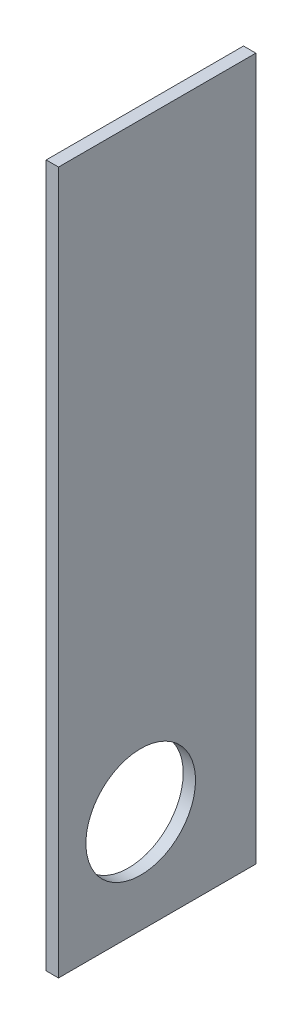
SolidWorks part; units mm, degrees
ref_plane "Front Plane" through (0, 0, 0) normal (0, 0, 1) x (1, 0, 0)
ref_plane "Top Plane" through (0, 0, 0) normal (0, 1, 0) x (1, 0, 0)
ref_plane "Right Plane" through (0, 0, 0) normal (1, 0, 0) x (0, 0, -1)
sketch "Sketch1" plane through (0, 0, 0) normal (1, 0, 0) x (0, 0, -1)
  line L1 (20.3921, -967.2196) -> (-267.6079, -967.2196)
  line L2 (20.3921, -967.2196) -> (20.3921, 57.7804)
  line L3 (20.3921, 57.7804) -> (-267.6079, 57.7804)
  line L4 (-267.6079, -967.2196) -> (-267.6079, -836.1219)
  line L5 (20.3921, -967.2196) -> (-267.6079, 57.7804) construction
  line L6 (20.3921, 57.7804) -> (-267.6079, -967.2196) construction
  line L7 (-267.6079, -676.1219) -> (-267.6079, 57.7804)
  line L10 (-267.6079, -676.1219) -> (-267.6079, -836.1219)
  circle A0 centre (-147.6079, -817.2196) radius 80
  point P0 (-123.6079, -454.7196)
  dimension "D3" = 160
  dimension "D4" = 120
  dimension "D1" = 288
  dimension "D2" = 1025
  dimension "D5" = 150
extrude "Boss-Extrude1" add sketch "Sketch1" along normal blind 18
equation "\"H_POLKI\"=1025"
equation "\"D2@Sketch1\"=\"H_POLKI\""
equation "\"DSP_WIDTH\"=18"
equation "\"D1@Boss-Extrude1\"=\"DSP_WIDTH\""
